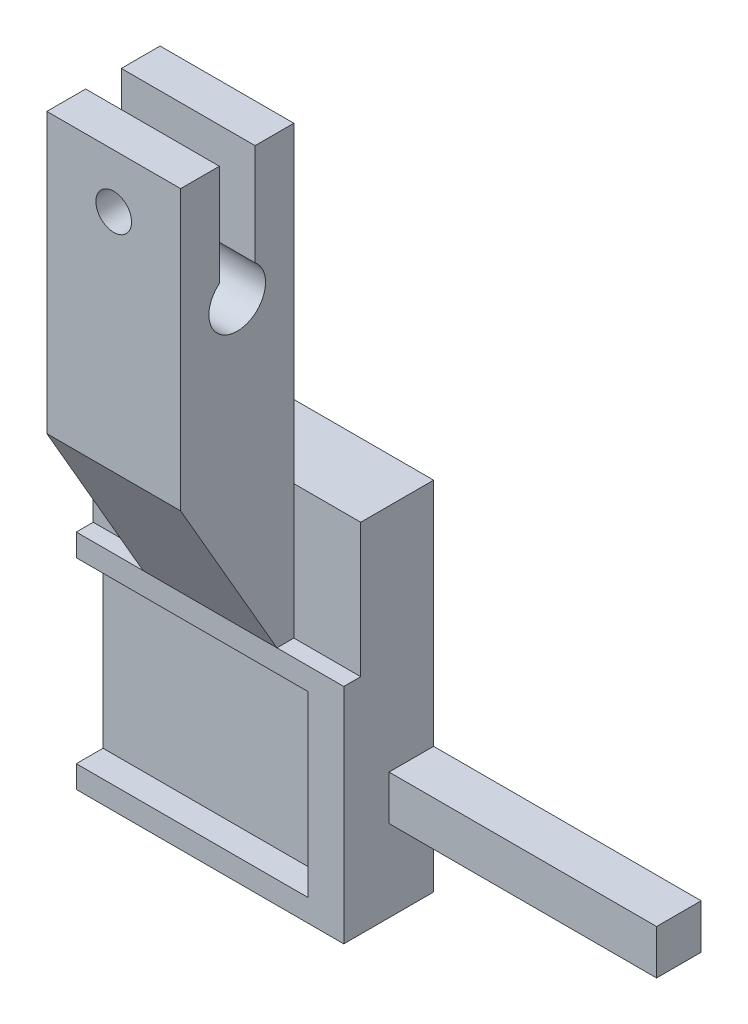
SolidWorks part; units mm, degrees
ref_plane "Front Plane" through (0, 0, 0) normal (0, 0, 1) x (1, 0, 0)
ref_plane "Top Plane" through (0, 0, 0) normal (0, 1, 0) x (1, 0, 0)
ref_plane "Right Plane" through (0, 0, 0) normal (1, 0, 0) x (0, 0, -1)
sketch "Sketch2" plane through (0, 0, 0) normal (1, 0, 0) x (0, 0, -1)
  line L0 (0, 0) -> (0, 40)
  line L1 (0, 40) -> (-8.175, 40)
  line L2 (-8.175, 40) -> (-8.175, 75)
  line L3 (-8.175, 75) -> (-20.875, 75)
  line L4 (-20.875, 75) -> (-20.875, 25)
  line L5 (-20.875, 25) -> (-8.175, 25)
  line L6 (-8.175, 25) -> (-8.175, 0)
  line L7 (-8.175, 0) -> (0, 0)
  dimension "D1" = 12.7
  dimension "D2" = 8.175
  dimension "D3" = 50
  dimension "D4" = 40
  dimension "D5" = 25
extrude "Boss-Extrude1" add sketch "Sketch2" along normal blind 15
sketch "Sketch7" plane through (0, 0, 0) normal (-1, 0, 0) x (0, 0, 1)
  line L0 (12.525, 75) -> (12.525, 63.6159)
  line L1 (8.175, 75) -> (20.875, 75) construction
  line L2 (16.525, 75) -> (16.525, 63.6159)
  line L3 (12.525, 75) -> (16.525, 75)
  line L5 (8.175, 25) -> (8.175, 0) construction
  arc A0 (12.525, 63.6159) -> (16.525, 63.6159) centre (14.525, 61.15) ccw
  point P1 (8.175, 12.5)
  point P8 (14.525, 75)
  point P12 (14.525, 75)
  dimension "D1" = 6.35
  dimension "D2" = 4
  dimension "D3" = 48.65
extrude "Cut-Extrude4" cut sketch "Sketch7" against normal through all
sketch "Sketch8" plane through (0, 0, 20.875) normal (0, 0, 1) x (1, 0, 0)
  line L0 (15, 75) -> (0, 75) construction
  circle A0 centre (7.5, 69) radius 2
  point P4 (7.5, 75)
  dimension "D1" = 4
  dimension "D2" = 6
extrude "Cut-Extrude5" cut sketch "Sketch8" against normal through all
sketch "Sketch9" plane through (0, 0, 0) normal (1, 0, 0) x (0, 0, -1)
  line L1 (-8.175, 40) -> (0, 40)
  line L2 (-8.175, 40) -> (-8.175, 0)
  line L3 (-8.175, 0) -> (0, 0)
  line L4 (0, 40) -> (0, 0)
extrude "Boss-Extrude2" add sketch "Sketch9" along normal blind 22.5 and the other way blind 7.5
sketch "Sketch11" plane through (-7.5, 0, 0) normal (-1, 0, 0) x (0, 0, 1)
  line L0 (8.175, 40) -> (8.175, 0) construction
  line L1 (7.075, 22.5) -> (8.175, 22.5)
  line L2 (7.075, 22.5) -> (7.075, 2.5)
  line L3 (7.075, 2.5) -> (8.175, 2.5)
  line L4 (8.175, 22.5) -> (8.175, 2.5)
  line L5 (8.175, 0) -> (0, 0) construction
  dimension "D1" = 20
  dimension "D2" = 2.5
  dimension "D3" = 1.1
extrude "Cut-Extrude6" cut sketch "Sketch11" against normal blind 26
sketch "Sketch12" plane through (-7.5, 0, 0) normal (-1, 0, 0) x (0, 0, 1)
  line L0 (10.075, 22.5) -> (7.075, 22.5)
  line L1 (10.075, 22.5) -> (10.075, 25)
  line L2 (10.075, 25) -> (5.075, 25)
  line L3 (5.075, 25) -> (5.075, 0)
  line L4 (5.075, 0) -> (10.075, 0)
  line L5 (7.075, 22.5) -> (7.075, 2.5) construction
  line L6 (10.075, 0) -> (10.075, 2.5)
  line L8 (7.075, 2.5) -> (7.075, 22.5)
  line L9 (8.175, 22.5) -> (7.075, 22.5) construction
  line L12 (7.075, 2.5) -> (10.075, 2.5)
  line L14 (8.175, 0) -> (0, 0) construction
  line L15 (20.875, 25) -> (8.175, 25) construction
  dimension "D1" = 3
  dimension "D2" = 2
  dimension "D3" = 3
extrude "Boss-Extrude4" add sketch "Sketch12" against normal through all
sketch "Sketch13" plane through (22.5, 0, 0) normal (1, 0, 0) x (0, 0, -1)
  line L0 (-10.075, 0) -> (0, 0) construction
  line L1 (-10.075, 25) -> (-8.175, 25)
  line L2 (-10.075, 25) -> (-10.075, 0)
  line L3 (-10.075, 0) -> (-8.175, 0)
  line L4 (-8.175, 25) -> (-8.175, 0)
extrude "Boss-Extrude5" add sketch "Sketch13" against normal up to surface (4 mm away) up to face at (18.5, 12.5, 7.625)
sketch "Sketch15" plane through (22.5, 0, 0) normal (1, 0, 0) x (0, 0, -1)
  line L1 (-5, 14.15) -> (0, 14.15)
  line L2 (-5, 14.15) -> (-5, 9.15)
  line L3 (-5, 9.15) -> (0, 9.15)
  line L4 (0, 14.15) -> (0, 9.15)
  arc A0 (-16.525, 63.6159) -> (-12.525, 63.6159) centre (-14.525, 61.15) ccw construction
  arc A1 (-16.525, 63.6159) -> (-12.525, 63.6159) centre (-14.525, 61.15) ccw construction
  point P4 (-14.525, 57.975)
  dimension "D2" = 47
  dimension "D1" = 9.525
  dimension "D3" = 5
  dimension "D4" = 5
extrude "Boss-Extrude6" add sketch "Sketch15" along normal blind 30
sketch "Sketch16" plane through (15, 0, 0) normal (1, 0, 0) x (0, 0, -1)
  line L0 (-10.075, 25) -> (-20.875, 43.7061)
  line L1 (-20.875, 75) -> (-20.875, 25) construction
  line L2 (-20.875, 43.7061) -> (-20.875, 25)
  line L3 (-20.875, 25) -> (-10.075, 25)
  dimension "D1" = 60
extrude "Cut-Extrude7" cut sketch "Sketch16" against normal through all
